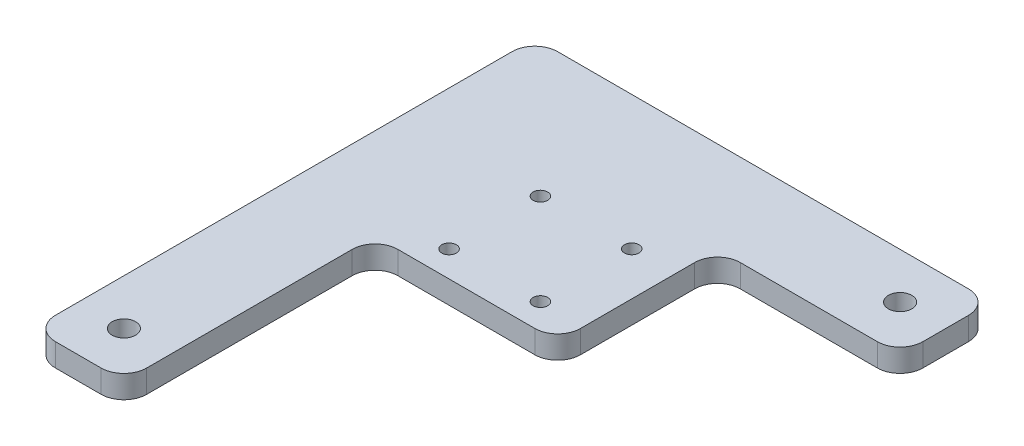
SolidWorks part; units mm, degrees
ref_plane "Front Plane" through (0, 0, 0) normal (0, 0, 1) x (1, 0, 0)
ref_plane "Top Plane" through (0, 0, 0) normal (0, 1, 0) x (1, 0, 0)
ref_plane "Right Plane" through (0, 0, 0) normal (1, 0, 0) x (0, 0, -1)
sketch "Sketch1" plane through (0, 0, 0) normal (0, 1, 0) x (1, 0, 0)
  line L0 (-53.9416, 54.0138) -> (73.0584, 54.0138)
  line L5 (22.2584, -15.8362) -> (-28.5416, -15.8362)
  line L6 (-28.5416, -15.8362) -> (-28.5416, -85.6862)
  line L7 (-53.9416, -85.6862) -> (-28.5416, -85.6862)
  line L8 (-53.9416, -85.6862) -> (-53.9416, 54.0138)
  line L10 (22.2584, -15.8362) -> (22.2584, 28.6138)
  line L11 (22.2584, 28.6138) -> (73.0584, 28.6138)
  line L12 (73.0584, 54.0138) -> (73.0584, 28.6138)
  circle A0 centre (10.2176, -8.5972) radius 2.0193 construction
  circle A1 centre (-15.1824, -8.5972) radius 2.0193 construction
  circle A2 centre (-15.1925, 16.8028) radius 2.0193 construction
  circle A3 centre (10.2075, 16.8028) radius 2.0193 construction
  circle A4 centre (-41.2416, -72.9862) radius 3.2639
  circle A5 centre (60.3584, 41.3138) radius 3.2639
  dimension "D10" = 4.0386
  dimension "D12" = 4.0386
  dimension "D14" = 4.0386
  dimension "D17" = 4.0386
  dimension "D21" = 6.5278
  dimension "D22" = 6.5278
  dimension "D2" = 12.7
  dimension "D3" = 62.8509
  dimension "D4" = 12.7
  dimension "D5" = 50.8
  dimension "D6" = 69.85
  dimension "D7" = 12.7
  dimension "D8" = 139.7
  dimension "D9" = 37.211
  dimension "D11" = 25.4
  dimension "D13" = 25.4
  dimension "D15" = 25.4
  dimension "D16" = 25.4
  dimension "D18" = 25.4
  dimension "D19" = 12.7
  dimension "D23" = 127
  dimension "D24" = 25.4
extrude "Boss-Extrude1" add sketch "Sketch1" along normal blind 6.35
fillet "Fillet1" radius 6.35 1 edges at (-28.5416, 3.175, 15.8362)
fillet "Fillet4" radius 6.35 1 edges at (-53.9416, 3.175, -54.0138)
fillet "Fillet5" radius 6.35 1 edges at (-53.9416, 3.175, 85.6862)
fillet "Fillet6" radius 6.35 1 edges at (-28.5416, 3.175, 85.6862)
fillet "Fillet9" radius 6.35 1 edges at (22.2584, 3.175, 15.8362)
fillet "Fillet10" radius 6.35 1 edges at (22.2584, 3.175, -28.6138)
fillet "Fillet11" radius 6.35 1 edges at (73.0584, 3.175, -28.6138)
fillet "Fillet12" radius 6.35 1 edges at (73.0584, 3.175, -54.0138)
hole_wizard "#21 (0.159) Diameter Hole1" positions "Sketch4" profile "Sketch5" hole size "#21" standard "ANSI Inch" end condition through all
sketch "Sketch4" plane through (0, 6.35, 0) normal (0, 1, 0) x (1, 0, 0)
  line L0 (66.7084, 54.0138) -> (-47.5916, 54.0138) construction
  line L2 (73.0584, 34.9638) -> (73.0584, 47.6638) construction
  point P0 (-15.1824, 16.8028)
  point P2 (-15.1824, -8.5972)
  point P4 (10.2176, -8.5972)
  point P6 (10.2176, 16.8028)
  dimension "D1" = 25.4
  dimension "D2" = 25.4
  dimension "D3" = 37.211
  dimension "D4" = 62.8408
sketch "Sketch5" plane through (-15.1824, 6.35, -16.8028) normal (1, 0, 0) x (0, 0, 1)
  line L0 (0, 0) -> (0, 6.35)
  line L1 (0, 6.35) -> (2.0193, 6.35)
  line L2 (2.0193, 6.35) -> (2.0193, 0)
  line L5 (2.0193, 0) -> (0, 0)
  line L11 (0, -6.35) -> (0, 107.95) construction
  dimension "Thru Hole Dia." = 4.0386
  dimension "Thru Hole Depth" = 6.35
